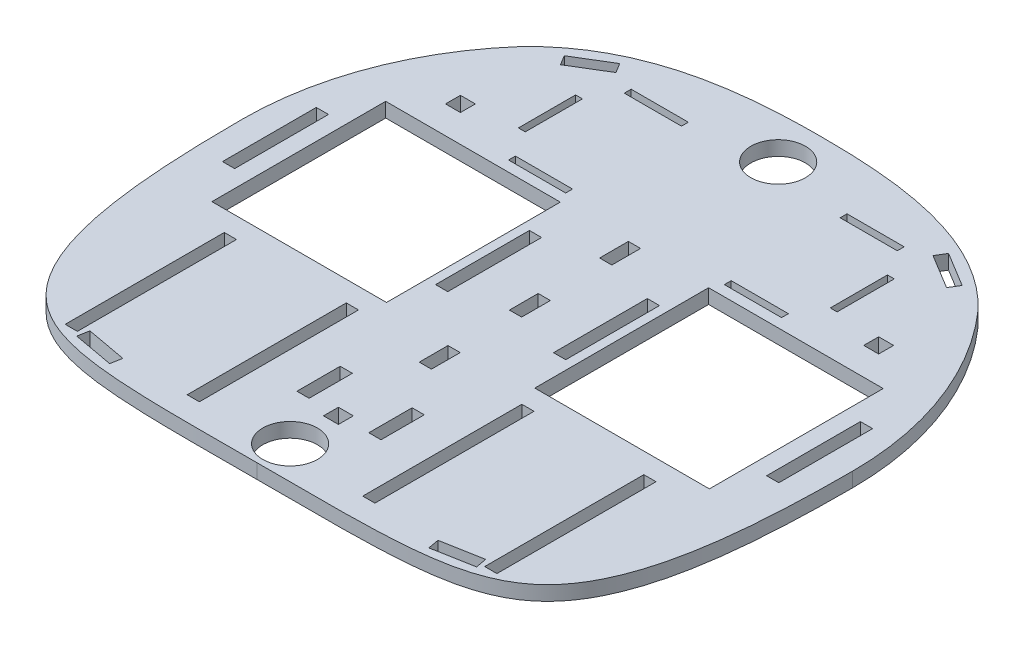
SolidWorks part; units mm, degrees
ref_plane "Front Plane" through (0, 0, 0) normal (0, 0, 1) x (1, 0, 0)
ref_plane "Top Plane" through (0, 0, 0) normal (0, 1, 0) x (1, 0, 0)
ref_plane "Right Plane" through (0, 0, 0) normal (1, 0, 0) x (0, 0, -1)
sketch "Sketch1" plane through (0, 0, 0) normal (0, 1, 0) x (1, 0, 0)
  line L0 (0, 0) -> (-157.9039, -157.9039) construction
  line L1 (0, -127) -> (0, 133.35) construction
  arc A0 (133.35, 0) -> (-133.35, 0) centre (0, 0) ccw
  spline S0 degree 3 poles (-133.35, 0) (-133.35, -51.198) (-123.8034, -129.8051) (-58.428, -127) (0, -127) knots 0 0 0 0 0.502616 1 1 1 1
  spline S1 degree 3 poles (133.35, 0) (133.35, -51.198) (123.8034, -129.8051) (58.428, -127) (0, -127) knots 0 0 0 0 0.502616 1 1 1 1
  dimension "D1" = 266.7
extrude "Base" add sketch "Sketch1" along normal blind 6.35
sketch "ShaftLayout" plane through (0, 6.35, 0) normal (0, 1, 0) x (1, 0, 0)
  line L0 (-133.35, 0) -> (133.35, 0) construction
  line L1 (0, 133.35) -> (0, -127) construction
  line L2 (-114.7053, -6.35) -> (-104.7993, -6.35)
  line L3 (-36.3853, -38) -> (-94.3853, -38)
  line L4 (-36.3853, -38) -> (-36.3853, 38)
  line L5 (-36.3853, 38) -> (-94.3853, 38)
  line L6 (-94.3853, -38) -> (-94.3853, 38)
  line L7 (-36.3853, -38) -> (-94.3853, 38) construction
  line L8 (-36.3853, 38) -> (-94.3853, -38) construction
  line L9 (-102.0053, -15.875) -> (-104.7993, -15.875)
  line L10 (-102.0053, -15.875) -> (-102.0053, 15.875)
  line L11 (-102.0053, 15.875) -> (-104.7993, 15.875)
  line L12 (-104.7993, -15.875) -> (-104.7993, 15.875)
  line L13 (-102.0053, -15.875) -> (-104.7993, 15.875) construction
  line L14 (-102.0053, 15.875) -> (-104.7993, -15.875) construction
  line L15 (-114.7053, -6.35) -> (-114.7053, 6.35)
  line L16 (-104.7993, -6.35) -> (-104.7993, 6.35)
  line L17 (-114.7053, 6.35) -> (-104.7993, 6.35)
  line L18 (-114.7053, -6.35) -> (-104.7993, 6.35) construction
  line L19 (-104.7993, -6.35) -> (-114.7053, 6.35) construction
  line L20 (-116.2928, -9.525) -> (-114.7053, -9.525)
  line L21 (-116.2928, -9.525) -> (-116.2928, 9.525)
  line L22 (-114.7053, -9.525) -> (-114.7053, 9.525)
  line L23 (-116.2928, 9.525) -> (-114.7053, 9.525)
  line L24 (-116.2928, -9.525) -> (-114.7053, 9.525) construction
  line L25 (-114.7053, -9.525) -> (-116.2928, 9.525) construction
  line L26 (-127.4053, -7.9375) -> (-116.2928, -7.9375)
  line L27 (-127.4053, -7.9375) -> (-127.4053, 7.9375)
  line L28 (-116.2928, -7.9375) -> (-116.2928, 7.9375)
  line L29 (-127.4053, 7.9375) -> (-116.2928, 7.9375)
  line L30 (-127.4053, -7.9375) -> (-116.2928, 7.9375) construction
  line L31 (-116.2928, -7.9375) -> (-127.4053, 7.9375) construction
  line L32 (-17.3353, -7.9375) -> (-28.4478, -7.9375)
  line L33 (-30.0353, -9.525) -> (-28.4478, -9.525)
  line L34 (-30.0353, -9.525) -> (-30.0353, 9.525)
  line L35 (-30.0353, 9.525) -> (-28.4478, 9.525)
  line L36 (-28.4478, -9.525) -> (-28.4478, 9.525)
  line L37 (-30.0353, -9.525) -> (-28.4478, 9.525) construction
  line L38 (-30.0353, 9.525) -> (-28.4478, -9.525) construction
  line L39 (-17.3353, -7.9375) -> (-17.3353, 7.9375)
  line L40 (-28.4478, -7.9375) -> (-28.4478, 7.9375)
  line L41 (-17.3353, 7.9375) -> (-28.4478, 7.9375)
  line L42 (-17.3353, -7.9375) -> (-28.4478, 7.9375) construction
  line L43 (-28.4478, -7.9375) -> (-17.3353, 7.9375) construction
  line L45 (-67.3853, -10.033) -> (-56.3853, -10.033)
  line L46 (-67.3853, -10.033) -> (-67.3853, 10.033)
  line L47 (-67.3853, 10.033) -> (-56.3853, 10.033)
  line L48 (-56.3853, -10.033) -> (-56.3853, 10.033)
  line L49 (-67.3853, -10.033) -> (-56.3853, 10.033) construction
  line L50 (-67.3853, 10.033) -> (-56.3853, -10.033) construction
  arc A0 (133.35, 0) -> (-133.35, 0) centre (0, 0) ccw construction
  point P10 (-65.3853, 0)
  point P15 (-103.4023, 0)
  point P20 (-29.2416, 0)
  point P21 (-109.7523, 0)
  point P22 (-115.4991, 0)
  point P23 (-121.8491, 0)
  point P40 (-61.8853, 0)
  point P41 (-22.8916, 0)
  dimension "D1" = 58
  dimension "D2" = 76
  dimension "D3" = 7.62
  dimension "D4" = 2.794
  dimension "D5" = 31.75
  dimension "D6" = 9.906
  dimension "D7" = 12.7
  dimension "D8" = 19.05
  dimension "D9" = 1.5875
  dimension "D10" = 12.7
  dimension "D11" = 15.875
  dimension "D12" = 19.05
  dimension "D13" = 1.5875
  dimension "D14" = 15.875
  dimension "D15" = 12.7
  dimension "D16" = 6.35
  dimension "D17" = 20.066
  dimension "D18" = 20
  dimension "D19" = 11
sketch "MotorLayout" plane through (0, 6.35, 0) normal (0, 1, 0) x (1, 0, 0)
  line L0 (-94.3853, -81.74) -> (-114.3853, -81.74) construction
  line L1 (-94.3853, -110.24) -> (-18.3853, -110.24)
  line L2 (-94.3853, -110.24) -> (-94.3853, -53.24)
  line L3 (-94.3853, -53.24) -> (-18.3853, -53.24)
  line L4 (-18.3853, -110.24) -> (-18.3853, -53.24)
  line L5 (-94.3853, -110.24) -> (-18.3853, -53.24) construction
  line L6 (-94.3853, -53.24) -> (-18.3853, -110.24) construction
  line L7 (-114.7053, -92.0587) -> (-104.7993, -92.0587)
  line L8 (-104.7993, -97.615) -> (-102.0053, -97.615)
  line L9 (-104.7993, -97.615) -> (-104.7993, -65.865)
  line L10 (-104.7993, -65.865) -> (-102.0053, -65.865)
  line L11 (-102.0053, -97.615) -> (-102.0053, -65.865)
  line L12 (-104.7993, -97.615) -> (-102.0053, -65.865) construction
  line L13 (-104.7993, -65.865) -> (-102.0053, -97.615) construction
  line L14 (-36.3853, -38) -> (-94.3853, -38) construction
  line L15 (-114.7053, -92.0587) -> (-114.7053, -71.4212)
  line L16 (-104.7993, -92.0587) -> (-104.7993, -71.4212)
  line L17 (-114.7053, -71.4212) -> (-104.7993, -71.4212)
  line L18 (-114.7053, -92.0587) -> (-104.7993, -71.4212) construction
  line L19 (-104.7993, -92.0587) -> (-114.7053, -71.4212) construction
  line L20 (-103.4023, -1000) -> (-103.4023, 49000) construction
  line L21 (-34.8953, -53.24) -> (-34.8953, -110.24) construction
  point P0 (-56.3853, -81.74)
  point P7 (-103.4023, -81.74)
  point P14 (-109.7523, -81.74)
  dimension "D1" = 20
  dimension "D2" = 76
  dimension "D3" = 57
  dimension "D4" = 2.794
  dimension "D5" = 15.24
  dimension "D6" = 31.75
  dimension "D7" = 20.6375
  dimension "D8" = 12.7
  dimension "D9" = 7.62
  dimension "D10" = 16.51
sketch "Sketch6" plane through (0, 6.35, 0) normal (0, 1, 0) x (1, 0, 0)
  line L0 (-36.3853, -38) -> (-36.3853, 38) construction
  line L1 (-32.4166, -38) -> (-108.7681, -38)
  line L2 (-32.4166, -38) -> (-32.4166, 38)
  line L3 (-32.4166, 38) -> (-108.7681, 38)
  line L4 (-108.7681, -38) -> (-108.7681, 38)
  line L5 (-28.4478, -9.525) -> (-28.4478, 9.525) construction
  line L6 (-104.7993, -15.875) -> (-104.7993, 15.875) construction
  line L7 (0, 133.35) -> (0, -127) construction
  line L8 (28.4478, 20.5105) -> (23.1138, -20.5105) construction
  line L9 (28.4478, -20.5105) -> (23.1138, 20.5105) construction
  line L10 (116.2928, 20.5105) -> (121.6268, -20.5105) construction
  line L11 (116.2928, -20.5105) -> (121.6268, 20.5105) construction
  line L12 (-133.35, 0) -> (133.35, 0) construction
  line L13 (-116.2928, -20.5105) -> (-121.6268, -20.5105)
  line L14 (-116.2928, -20.5105) -> (-116.2928, 20.5105)
  line L15 (-116.2928, 20.5105) -> (-121.6268, 20.5105)
  line L16 (-121.6268, -20.5105) -> (-121.6268, 20.5105)
  line L17 (-116.2928, -20.5105) -> (-121.6268, 20.5105) construction
  line L18 (-116.2928, 20.5105) -> (-121.6268, -20.5105) construction
  line L19 (-116.2928, -9.525) -> (-116.2928, 9.525) construction
  line L20 (-127.4053, 7.9375) -> (-116.2928, 7.9375) construction
  line L21 (-17.3353, 7.9375) -> (-28.4478, 7.9375) construction
  line L22 (-28.4478, -20.5105) -> (-23.1138, -20.5105)
  line L23 (-28.4478, -20.5105) -> (-28.4478, 20.5105)
  line L24 (-28.4478, 20.5105) -> (-23.1138, 20.5105)
  line L25 (-23.1138, -20.5105) -> (-23.1138, 20.5105)
  line L26 (-28.4478, -20.5105) -> (-23.1138, 20.5105) construction
  line L27 (-28.4478, 20.5105) -> (-23.1138, -20.5105) construction
  line L28 (23.1138, -20.5105) -> (23.1138, 20.5105)
  line L29 (28.4478, 20.5105) -> (23.1138, 20.5105)
  line L30 (28.4478, -20.5105) -> (28.4478, 20.5105)
  line L31 (28.4478, -20.5105) -> (23.1138, -20.5105)
  line L32 (121.6268, -20.5105) -> (121.6268, 20.5105)
  line L33 (116.2928, 20.5105) -> (121.6268, 20.5105)
  line L34 (116.2928, -20.5105) -> (116.2928, 20.5105)
  line L35 (116.2928, -20.5105) -> (121.6268, -20.5105)
  line L36 (108.7681, -38) -> (108.7681, 38)
  line L37 (32.4166, 38) -> (108.7681, 38)
  line L38 (32.4166, -38) -> (32.4166, 38)
  line L39 (32.4166, -38) -> (108.7681, -38)
  point P16 (-118.9598, 0)
  point P27 (-25.7808, 0)
  point P44 (25.7808, 0)
  point P45 (118.9598, 0)
  dimension "D1" = 3.9688
  dimension "D2" = 3.9688
  dimension "D3" = 12.573
  dimension "D4" = 12.573
  dimension "D5" = 5.334
  dimension "D6" = 5.334
extrude "WheelShaftCut" cut sketch "Sketch6" against normal through all
sketch "Sketch8" plane through (0, 6.35, 0) normal (0, 1, 0) x (1, 0, 0)
  line L0 (-94.3853, -81.74) -> (-18.3853, -81.74) construction
  line L1 (-18.3853, -110.24) -> (-18.3853, -53.24) construction
  line L2 (-94.3853, -53.24) -> (-18.3853, -53.24) construction
  line L3 (-35.7113, -116.5265) -> (-41.0453, -116.5265)
  line L4 (-35.7113, -116.5265) -> (-35.7113, -46.9535)
  line L5 (-35.7113, -46.9535) -> (-41.0453, -46.9535)
  line L6 (-41.0453, -116.5265) -> (-41.0453, -46.9535)
  line L7 (-35.7113, -116.5265) -> (-41.0453, -46.9535) construction
  line L8 (-35.7113, -46.9535) -> (-41.0453, -116.5265) construction
  line L9 (18.3853, -72.2785) -> (13.0513, -91.2015) construction
  line L10 (18.3853, -91.2015) -> (13.0513, -72.2785) construction
  line L11 (18.3853, -81.74) -> (15.7183, -81.74) construction
  line L12 (89.0513, -46.9535) -> (94.3853, -116.5265) construction
  line L13 (89.0513, -116.5265) -> (94.3853, -46.9535) construction
  line L14 (35.7113, -46.9535) -> (41.0453, -116.5265) construction
  line L15 (-89.0513, -116.5265) -> (-94.3853, -116.5265)
  line L16 (-89.0513, -116.5265) -> (-89.0513, -46.9535)
  line L17 (-89.0513, -46.9535) -> (-94.3853, -46.9535)
  line L18 (-94.3853, -116.5265) -> (-94.3853, -46.9535)
  line L19 (-89.0513, -116.5265) -> (-94.3853, -46.9535) construction
  line L20 (-89.0513, -46.9535) -> (-94.3853, -116.5265) construction
  line L21 (-94.3853, -110.24) -> (-94.3853, -53.24) construction
  line L22 (0, 133.35) -> (0, -127) construction
  line L23 (35.7113, -116.5265) -> (41.0453, -46.9535) construction
  line L24 (94.3853, -81.74) -> (18.3853, -81.74) construction
  line L25 (13.0513, -91.2015) -> (13.0513, -72.2785)
  line L26 (18.3853, -72.2785) -> (13.0513, -72.2785)
  line L27 (18.3853, -91.2015) -> (18.3853, -72.2785)
  line L28 (18.3853, -91.2015) -> (13.0513, -91.2015)
  line L29 (94.3853, -116.5265) -> (94.3853, -46.9535)
  line L30 (89.0513, -46.9535) -> (94.3853, -46.9535)
  line L31 (89.0513, -116.5265) -> (89.0513, -46.9535)
  line L32 (89.0513, -116.5265) -> (94.3853, -116.5265)
  line L33 (41.0453, -116.5265) -> (41.0453, -46.9535)
  line L34 (35.7113, -46.9535) -> (41.0453, -46.9535)
  line L35 (35.7113, -116.5265) -> (35.7113, -46.9535)
  line L36 (35.7113, -116.5265) -> (41.0453, -116.5265)
  line L37 (-94.3853, -110.24) -> (-18.3853, -110.24) construction
  line L42 (-18.3853, -81.74) -> (-15.7183, -81.74) construction
  line L44 (-18.3853, -91.2015) -> (-13.0513, -91.2015)
  line L45 (-18.3853, -91.2015) -> (-18.3853, -72.2785)
  line L46 (-18.3853, -72.2785) -> (-13.0513, -72.2785)
  line L47 (-13.0513, -91.2015) -> (-13.0513, -72.2785)
  line L48 (-18.3853, -91.2015) -> (-13.0513, -72.2785) construction
  line L49 (-18.3853, -72.2785) -> (-13.0513, -91.2015) construction
  point P6 (-63.7079, -81.74)
  point P7 (-38.2513, -81.74)
  point P19 (-91.5913, -81.74)
  point P39 (91.5913, -81.74)
  point P40 (38.2513, -81.74)
  dimension "D1" = 5.334
  dimension "D2" = 6.2865
  dimension "D4" = 5.334
  dimension "D5" = 18.923
  dimension "D6" = 6.2865
  dimension "D3" = 2
extrude "MotorCut" cut sketch "Sketch8" against normal through all
sketch "BatteryLayout" plane through (0, 6.35, 0) normal (0, 1, 0) x (1, 0, 0)
  line L0 (0, 133.35) -> (0, -127) construction
  line L1 (-32.4166, 38) -> (-108.7681, 38) construction
  line L2 (-66.675, 45.62) -> (66.675, 45.62)
  line L3 (-66.675, 45.62) -> (-66.675, 93.245)
  line L4 (-66.675, 93.245) -> (66.675, 93.245)
  line L5 (66.675, 45.62) -> (66.675, 93.245)
  line L6 (-66.675, 45.62) -> (66.675, 93.245) construction
  line L7 (-66.675, 93.245) -> (66.675, 45.62) construction
  arc A0 (133.35, 0) -> (-133.35, 0) centre (0, 0) ccw construction
  point P6 (0, 69.4325)
  dimension "D1" = 133.35
  dimension "D2" = 47.625
  dimension "D3" = 7.62
sketch "Sketch10" plane through (0, 6.35, 0) normal (0, 1, 0) x (1, 0, 0)
  line L0 (-66.675, 93.245) -> (66.675, 93.245) construction
  line L1 (-59.69, 42.62) -> (-34.69, 42.62)
  line L2 (-59.69, 42.62) -> (-59.69, 45.62)
  line L3 (-59.69, 45.62) -> (-34.69, 45.62)
  line L4 (-34.69, 42.62) -> (-34.69, 45.62)
  line L5 (-59.69, 42.62) -> (-34.69, 45.62) construction
  line L6 (-59.69, 45.62) -> (-34.69, 42.62) construction
  line L7 (-59.69, 96.245) -> (-34.69, 96.245)
  line L8 (-59.69, 96.245) -> (-59.69, 93.245)
  line L9 (-59.69, 93.245) -> (-34.69, 93.245)
  line L10 (-34.69, 96.245) -> (-34.69, 93.245)
  line L11 (-59.69, 96.245) -> (-34.69, 93.245) construction
  line L12 (-59.69, 93.245) -> (-34.69, 96.245) construction
  line L13 (-66.675, 45.62) -> (66.675, 45.62) construction
  line L14 (-66.675, 45.62) -> (-66.675, 93.245) construction
  line L15 (0, 69.4325) -> (-66.675, 69.4325) construction
  line L16 (-66.675, 56.9325) -> (-69.675, 56.9325)
  line L17 (-66.675, 56.9325) -> (-66.675, 81.9325)
  line L18 (-66.675, 81.9325) -> (-69.675, 81.9325)
  line L19 (-69.675, 56.9325) -> (-69.675, 81.9325)
  line L20 (0, 133.35) -> (0, -127) construction
  line L21 (59.69, 93.245) -> (34.69, 96.245) construction
  line L22 (59.69, 96.245) -> (34.69, 93.245) construction
  line L23 (59.69, 45.62) -> (34.69, 42.62) construction
  line L24 (59.69, 42.62) -> (34.69, 45.62) construction
  line L25 (69.675, 56.9325) -> (69.675, 81.9325)
  line L26 (66.675, 81.9325) -> (69.675, 81.9325)
  line L27 (66.675, 56.9325) -> (66.675, 81.9325)
  line L28 (66.675, 56.9325) -> (69.675, 56.9325)
  line L29 (34.69, 96.245) -> (34.69, 93.245)
  line L30 (59.69, 93.245) -> (34.69, 93.245)
  line L31 (59.69, 96.245) -> (59.69, 93.245)
  line L32 (59.69, 96.245) -> (34.69, 96.245)
  line L33 (34.69, 42.62) -> (34.69, 45.62)
  line L34 (59.69, 45.62) -> (34.69, 45.62)
  line L35 (59.69, 42.62) -> (59.69, 45.62)
  line L36 (59.69, 42.62) -> (34.69, 42.62)
  point P0 (-47.19, 44.12)
  point P5 (-47.19, 94.745)
  point P20 (-66.675, 69.4325)
  point P40 (66.675, 69.4325)
  point P41 (47.19, 94.745)
  point P42 (47.19, 44.12)
  dimension "D1" = 3
  dimension "D2" = 3
  dimension "D3" = 25
  dimension "D4" = 25
  dimension "D5" = 6.985
  dimension "D6" = 6.985
  dimension "D7" = 3
  dimension "D8" = 25
extrude "VelcroCut" cut sketch "Sketch10" against normal through all
sketch "Sketch11" plane through (0, 6.35, 0) normal (0, 1, 0) x (1, 0, 0)
  line L0 (0, 133.35) -> (0, -127) construction
  line L1 (-133.35, 0) -> (133.35, 0) construction
  line L3 (-94.7039, 50.0761) -> (-88.1761, 50.0761)
  line L4 (-94.7039, 50.0761) -> (-94.7039, 56.6039)
  line L5 (-94.7039, 56.6039) -> (-88.1761, 56.6039)
  line L6 (-88.1761, 50.0761) -> (-88.1761, 56.6039)
  line L7 (-94.7039, 50.0761) -> (-88.1761, 56.6039) construction
  line L8 (-94.7039, 56.6039) -> (-88.1761, 50.0761) construction
  line L9 (88.1761, 50.0761) -> (94.7039, 50.0761)
  line L10 (88.1761, 50.0761) -> (88.1761, 56.6039)
  line L11 (88.1761, 56.6039) -> (94.7039, 56.6039)
  line L12 (94.7039, 50.0761) -> (94.7039, 56.6039)
  line L13 (88.1761, 50.0761) -> (94.7039, 56.6039) construction
  line L14 (88.1761, 56.6039) -> (94.7039, 50.0761) construction
  line L15 (-3.2639, -94.7039) -> (3.2639, -94.7039)
  line L16 (-3.2639, -94.7039) -> (-3.2639, -88.1761)
  line L17 (-3.2639, -88.1761) -> (3.2639, -88.1761)
  line L18 (3.2639, -94.7039) -> (3.2639, -88.1761)
  line L19 (-3.2639, -94.7039) -> (3.2639, -88.1761) construction
  line L20 (-3.2639, -88.1761) -> (3.2639, -94.7039) construction
  circle A1 centre (0, -91.44) radius 3.175 construction
  circle A2 centre (-91.44, 53.34) radius 3.175 construction
  circle A3 centre (91.44, 53.34) radius 3.175 construction
  dimension "D1" = 6.35
  dimension "D2" = 53.34
  dimension "D3" = 6.35
  dimension "D6" = 91.44
  dimension "D5" = 6.5278
  dimension "D4" = 91.44
  dimension "D7" = 6.5278
  dimension "D8" = 6.5278
  dimension "D9" = 6.5278
  dimension "D10" = 6.5278
  dimension "D11" = 6.5278
extrude "ScrewCut" cut sketch "Sketch11" against normal through all
sketch "Sketch13" plane through (0, 6.35, 0) normal (0, 1, 0) x (1, 0, 0)
  line L0 (0, 133.35) -> (0, -127) construction
  line L1 (-2.667, 25.427) -> (2.667, 25.427)
  line L2 (-2.667, 25.427) -> (-2.667, 38)
  line L3 (-2.667, 38) -> (2.667, 38)
  line L4 (2.667, 25.427) -> (2.667, 38)
  line L5 (-2.667, 25.427) -> (2.667, 38) construction
  line L6 (-2.667, 38) -> (2.667, 25.427) construction
  line L7 (108.7681, 38) -> (32.4166, 38) construction
  line L8 (-2.667, -14.0065) -> (2.667, -14.0065)
  line L9 (-2.667, -14.0065) -> (-2.667, -1.4335)
  line L10 (-2.667, -1.4335) -> (2.667, -1.4335)
  line L11 (2.667, -14.0065) -> (2.667, -1.4335)
  line L12 (-2.667, -14.0065) -> (2.667, -1.4335) construction
  line L13 (-2.667, -1.4335) -> (2.667, -14.0065) construction
  line L14 (-2.667, -53.44) -> (2.667, -53.44)
  line L15 (-2.667, -53.44) -> (-2.667, -40.867)
  line L16 (-2.667, -40.867) -> (2.667, -40.867)
  line L17 (2.667, -53.44) -> (2.667, -40.867)
  line L18 (-2.667, -53.44) -> (2.667, -40.867) construction
  line L19 (-2.667, -40.867) -> (2.667, -53.44) construction
  point P0 (0, 31.7135)
  point P10 (0, -7.72)
  point P15 (0, -47.1535)
  dimension "D1" = 5.334
  dimension "D2" = 12.573
  dimension "D3" = 0
  dimension "D5" = 91.44
  dimension "D4" = 3
extrude "SupportStrutCut" cut sketch "Sketch13" against normal through all
sketch "Sketch16" plane through (0, 6.35, 0) normal (0, 1, 0) x (1, 0, 0)
  line L0 (0, -1000) -> (0, 49000) construction
  line L1 (-100.0331, 133.35) -> (-100.0331, 88.1793)
  line L2 (-100.0331, 133.35) -> (100.0331, 133.35)
  line L3 (100.0331, 133.35) -> (100.0331, 88.1793)
  arc A0 (133.35, 0) -> (-133.35, 0) centre (0, 0) ccw construction
  spline S0 degree 3 poles (-100.0331, 88.1793) (-73.9195, 115.9102) (-34.9729, 119.8228) (0, 119.8228) knots 0 0 0 0 1 1 1 1
  spline S1 degree 3 poles (100.0331, 88.1793) (73.9195, 115.9102) (34.9729, 119.8228) (0, 119.8228) knots 0 0 0 0 1 1 1 1
extrude "EmptySpaceTrim" cut sketch "Sketch16" against normal through all
sketch "Sketch15" plane through (0, 6.35, 0) normal (0, 1, 0) x (1, 0, 0)
  line L0 (-78.1477, -1116.59) -> (-78.1477, 48883.41) construction
  line L2 (-87.4187, -118.4593) -> (-69.7657, -121.6799)
  line L3 (-87.4187, -118.4593) -> (-86.5298, -113.5867)
  line L4 (-69.7657, -121.6799) -> (-68.8768, -116.8073)
  line L5 (-86.5298, -113.5867) -> (-68.8768, -116.8073)
  line L6 (-87.4187, -118.4593) -> (-68.8768, -116.8073) construction
  line L7 (-69.7657, -121.6799) -> (-86.5298, -113.5867) construction
  line L8 (-84.4066, 90.0604) -> (-69.3179, 99.2234)
  line L9 (-84.4066, 90.0604) -> (-86.9775, 94.2939)
  line L10 (-69.3179, 99.2234) -> (-71.8889, 103.4569)
  line L11 (-86.9775, 94.2939) -> (-71.8889, 103.4569)
  line L12 (-84.4066, 90.0604) -> (-71.8889, 103.4569) construction
  line L13 (-69.3179, 99.2234) -> (-86.9775, 94.2939) construction
  line L14 (0, -1000) -> (0, 49000) construction
  line L15 (69.3179, 99.2234) -> (86.9775, 94.2939) construction
  line L16 (84.4066, 90.0604) -> (71.8889, 103.4569) construction
  line L17 (69.7657, -121.6799) -> (86.5298, -113.5867) construction
  line L18 (87.4187, -118.4593) -> (68.8768, -116.8073) construction
  line L19 (88.7973, -116.59) -> (66.5019, -116.59) construction
  line L20 (86.9775, 94.2939) -> (71.8889, 103.4569)
  line L21 (69.3179, 99.2234) -> (71.8889, 103.4569)
  line L22 (84.4066, 90.0604) -> (86.9775, 94.2939)
  line L23 (84.4066, 90.0604) -> (69.3179, 99.2234)
  line L24 (86.5298, -113.5867) -> (68.8768, -116.8073)
  line L25 (69.7657, -121.6799) -> (68.8768, -116.8073)
  line L26 (87.4187, -118.4593) -> (86.5298, -113.5867)
  line L27 (87.4187, -118.4593) -> (69.7657, -121.6799)
  point P4 (-78.1477, 96.7587)
  point P7 (-78.1477, -117.6333)
  point P30 (78.1477, -117.6333)
  point P31 (78.1477, 96.7587)
  dimension "D1" = 4.953
  dimension "D2" = 17.653
  dimension "D3" = 17.653
  dimension "D4" = 4.953
extrude "TapeSensorCut" cut sketch "Sketch15" against normal through all
sketch "Sketch17" plane through (0, 6.35, 0) normal (0, 1, 0) x (1, 0, 0)
  line L0 (0, -1000) -> (0, 49000) construction
  line L1 (-34.69, 93.245) -> (34.69, 93.245) construction
  circle A0 centre (0, 100.8346) radius 11.938
  circle A1 centre (0, 100.8346) radius 5 construction
  circle A2 centre (0, -112.5625) radius 11.938
  dimension "D1" = 23.876
  dimension "D2" = 10
  dimension "D3" = 23.876
extrude "CasterCut" cut sketch "Sketch17" against normal through all
sketch "Layer1Limits" plane through (0, 0, 0) normal (0, 1, 0) x (1, 0, 0)
  line L0 (-127, 119.8228) -> (127, -134.1772) construction
  line L1 (-127, -134.1772) -> (127, -134.1772) construction
  line L2 (-127, -134.1772) -> (-127, 119.8228) construction
  line L3 (-127, 119.8228) -> (127, 119.8228) construction
  line L4 (127, -134.1772) -> (127, 119.8228) construction
  line L5 (127, 119.8228) -> (-127, -134.1772) construction
  line L6 (0, -1000) -> (0, 49000) construction
  point P4 (0, -7.1772)
  dimension "D1" = 254
  dimension "D2" = 254
